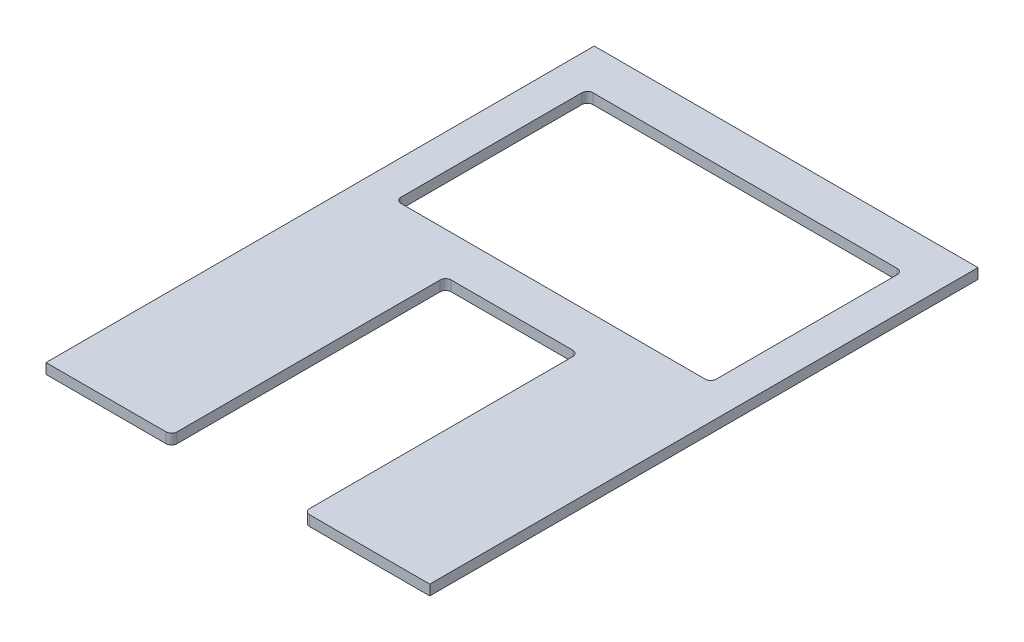
SolidWorks part; units mm, degrees
material "Delrin 2700 NC010, Low Viscosity Acetal Copolymer (SS)"
ref_plane "Front Plane" through (0, 0, 0) normal (0, 0, 1) x (1, 0, 0)
ref_plane "Top Plane" through (0, 0, 0) normal (0, 1, 0) x (1, 0, 0)
ref_plane "Right Plane" through (0, 0, 0) normal (1, 0, 0) x (0, 0, -1)
sketch "Sketch1" plane through (0, 0, 0) normal (0, 1, 0) x (1, 0, 0)
  line L0 (-30.734, -127) -> (-30.734, 0)
  line L1 (88.9, 127) -> (-88.9, 127)
  line L2 (88.9, 127) -> (88.9, -127)
  line L3 (88.9, -127) -> (30.734, -127)
  line L4 (-88.9, 127) -> (-88.9, -127)
  line L5 (88.9, 127) -> (-88.9, -127) construction
  line L6 (88.9, -127) -> (-88.9, 127) construction
  line L7 (-30.734, 0) -> (30.734, 0)
  line L8 (30.734, 0) -> (30.734, -127)
  line L9 (-30.734, -127) -> (-88.9, -127)
  line L10 (0, 0) -> (0, 127) construction
  line L12 (73.025, 107.95) -> (-73.025, 107.95)
  line L13 (73.025, 107.95) -> (73.025, 19.05)
  line L14 (73.025, 19.05) -> (-73.025, 19.05)
  line L15 (-73.025, 107.95) -> (-73.025, 19.05)
  line L16 (73.025, 107.95) -> (-73.025, 19.05) construction
  line L17 (73.025, 19.05) -> (-73.025, 107.95) construction
  point P0 (0, 0)
  point P12 (0, 63.5)
  dimension "D1" = 254
  dimension "D2" = 177.8
  dimension "D3" = 61.468
  dimension "D4" = 58.166
  dimension "D5" = 127
  dimension "D6" = 88.9
  dimension "D7" = 146.05
extrude "Boss-Extrude1" add sketch "Sketch1" along normal blind 4.7625
fillet "Fillet1" radius 2.54 8 edges at (30.734, 2.3813, 127) (-30.734, 2.3813, 127) (-30.734, 2.3813, 0) (30.734, 2.3813, 0) (-73.025, 2.3813, -19.05) (73.025, 2.3813, -19.05) (73.025, 2.3813, -107.95) (-73.025, 2.3813, -107.95)
